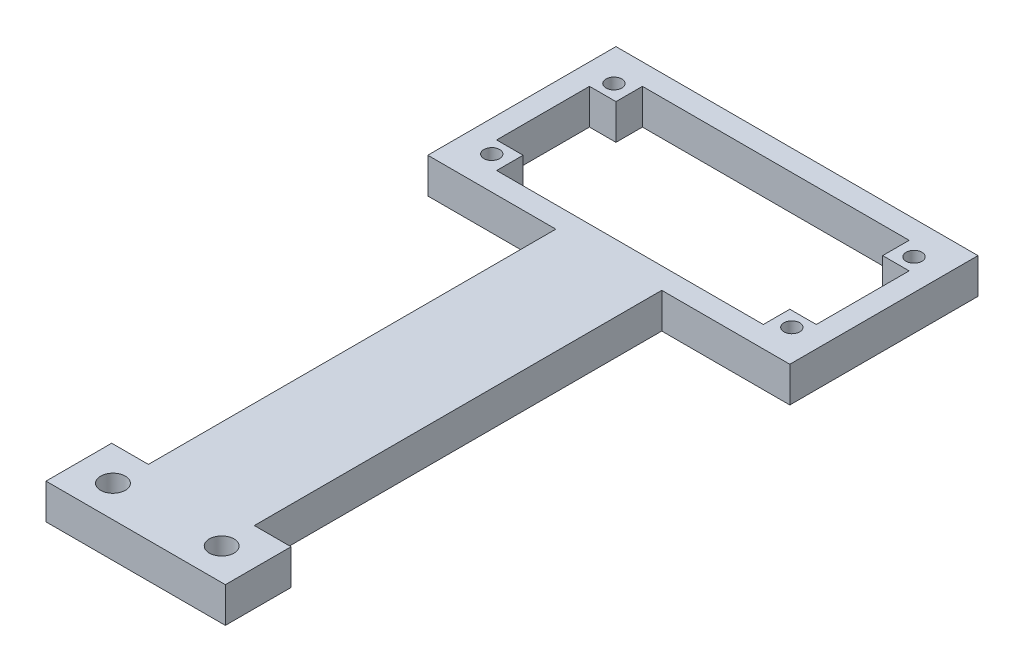
SolidWorks part; units mm, degrees
ref_plane "Front Plane" through (0, 0, 0) normal (0, 0, 1) x (1, 0, 0)
ref_plane "Top Plane" through (0, 0, 0) normal (0, 1, 0) x (1, 0, 0)
ref_plane "Right Plane" through (0, 0, 0) normal (1, 0, 0) x (0, 0, -1)
sketch "Sonic Sensor Reference Sketch" plane through (0, 0, 0) normal (0, 1, 0) x (1, 0, 0)
  line L1 (0, 0) -> (45.27, 0) construction
  line L2 (0, 0) -> (0, 20.65) construction
  line L3 (0, 20.65) -> (45.27, 20.65) construction
  line L4 (45.27, 0) -> (45.27, 20.65) construction
  dimension "D1" = 45.27
  dimension "D2" = 20.65
sketch "Sketch2" plane through (0, 0, 0) normal (0, 1, 0) x (1, 0, 0)
  line L8 (48.27, -3) -> (48.27, 23.65)
  line L9 (-3, -3) -> (48.27, -3)
  line L10 (-3, 23.65) -> (-3, -3)
  line L11 (48.27, 23.65) -> (-3, 23.65)
  line L12 (48.27, -3) -> (48.27, 23.65)
  line L13 (-3, -3) -> (48.27, -3)
  line L14 (-3, 23.65) -> (-3, -3)
  line L15 (48.27, 23.65) -> (-3, 23.65)
  dimension "D1" = 3
extrude "Boss-Extrude2" add sketch "Sketch2" along normal blind 5
sketch "Sketch3" plane through (0, 5, 0) normal (0, 1, 0) x (1, 0, 0)
  line L0 (0, 0) -> (45.27, 0) construction
  line L1 (45.27, 0) -> (45.27, 20.65) construction
  line L2 (0, 20.65) -> (45.27, 20.65) construction
  line L3 (0, 0) -> (0, 20.65) construction
  line L4 (0, 0) -> (45.27, 0)
  line L5 (45.27, 0) -> (45.27, 20.65)
  line L6 (0, 20.65) -> (45.27, 20.65)
  line L7 (0, 0) -> (0, 20.65)
extrude "Cut-Extrude1" cut sketch "Sketch3" against normal through all
sketch "Sketch4" plane through (0, 5, 0) normal (0, 1, 0) x (1, 0, 0)
  line L0 (1.385, 18.975) -> (43.885, 18.975) construction
  line L1 (22.635, 23.65) -> (22.635, -3) construction
  line L2 (48.27, 23.65) -> (-3, 23.65) construction
  line L3 (-3, -3) -> (48.27, -3) construction
  line L4 (-3, 10.325) -> (48.27, 10.325) construction
  line L5 (-3, 23.65) -> (-3, -3) construction
  line L6 (48.27, -3) -> (48.27, 23.65) construction
  line L7 (1.385, 18.975) -> (1.385, 1.675) construction
  line L8 (1.385, 1.675) -> (43.885, 1.675) construction
  line L9 (43.885, 1.675) -> (43.885, 18.975) construction
  line L11 (0, 20.65) -> (3.75, 20.65)
  line L12 (0, 20.65) -> (0, 16.9)
  line L13 (0, 16.9) -> (3.75, 16.9)
  line L14 (3.75, 20.65) -> (3.75, 16.9)
  line L15 (0, 0) -> (3.75, 0)
  line L16 (0, 0) -> (0, 3.75)
  line L17 (0, 3.75) -> (3.75, 3.75)
  line L18 (3.75, 0) -> (3.75, 3.75)
  line L19 (45.27, 0) -> (41.52, 0)
  line L20 (45.27, 0) -> (45.27, 3.75)
  line L21 (45.27, 3.75) -> (41.52, 3.75)
  line L22 (41.52, 0) -> (41.52, 3.75)
  line L23 (45.27, 20.65) -> (41.52, 20.65)
  line L24 (45.27, 20.65) -> (45.27, 16.9)
  line L25 (45.27, 16.9) -> (41.52, 16.9)
  line L26 (41.52, 20.65) -> (41.52, 16.9)
  circle A0 centre (1.385, 18.975) radius 1.12 construction
  circle A1 centre (43.885, 18.975) radius 1.12 construction
  circle A2 centre (1.385, 1.675) radius 1.12 construction
  circle A3 centre (43.885, 1.675) radius 1.12 construction
  point P17 (22.635, 18.975)
  point P18 (1.385, 10.325)
  dimension "D3" = 2.24
  dimension "D1" = 42.5
  dimension "D2" = 17.3
  dimension "D4" = 3.75
  dimension "D5" = 3.75
extrude "Boss-Extrude3" add sketch "Sketch4" against normal up to surface (5 mm away) up to face at (22.635, 0, -10.325)
sketch "Sketch5" plane through (0, 5, 0) normal (0, 1, 0) x (1, 0, 0)
  circle A0 centre (1.385, 18.975) radius 1.12
  circle A1 centre (43.885, 18.975) radius 1.12
  circle A2 centre (43.885, 1.675) radius 1.12
  circle A3 centre (1.385, 1.675) radius 1.12
  circle A4 centre (1.385, 18.975) radius 1.12 construction
  circle A5 centre (43.885, 18.975) radius 1.12 construction
  circle A6 centre (1.385, 1.675) radius 1.12 construction
  circle A7 centre (43.885, 1.675) radius 1.12 construction
extrude "Cut-Extrude2" cut sketch "Sketch5" against normal through all
sketch "Sketch6" plane through (0, 5, 0) normal (0, 1, 0) x (1, 0, 0)
  line L0 (-3, -3) -> (48.27, -3) construction
  line L1 (30.135, -3) -> (15.135, -3)
  line L2 (30.135, -3) -> (30.135, -60.7)
  line L3 (30.135, -60.7) -> (15.135, -60.7)
  line L4 (15.135, -3) -> (15.135, -60.7)
  point P6 (22.635, -3)
  point P7 (22.635, -3)
  dimension "D1" = 15
  dimension "D2" = 57.7
extrude "Boss-Extrude4" add sketch "Sketch6" against normal up to surface (5 mm away) up to face at (1.385, 0, -0.555)
sketch "Sketch7" plane through (0, 5, 0) normal (0, 1, 0) x (1, 0, 0)
  line L0 (15.135, -60.7) -> (30.135, -60.7) construction
  line L1 (9.935, -60.7) -> (35.335, -60.7)
  line L2 (9.935, -60.7) -> (9.935, -70.2)
  line L3 (9.935, -70.2) -> (35.335, -70.2)
  line L4 (35.335, -60.7) -> (35.335, -70.2)
  point P4 (22.635, -60.7)
  point P7 (22.635, -60.7)
  dimension "D1" = 25.4
  dimension "D2" = 9.5
extrude "Boss-Extrude5" add sketch "Sketch7" against normal up to surface (5 mm away) up to face at (1.385, 0, -0.555)
sketch "Sketch11" plane through (0, 0, 0) normal (0, -1, 0) x (1, 0, 0)
  circle A0 centre (30.335, 65.5178) radius 1.75
  circle A1 centre (14.935, 65.5178) radius 1.75
  dimension "D1" = 3.5
  dimension "D2" = 3.5
extrude "Cut-Extrude5" cut sketch "Sketch11" against normal through all
sketch "Sketch12" plane through (0, 5, 0) normal (0, 1, 0) x (1, 0, 0)
  line L0 (35.335, -70.2) -> (35.335, -60.7) construction
  line L1 (9.935, -70.2) -> (35.335, -70.2)
  line L2 (9.935, -70.2) -> (9.935, -70)
  line L3 (9.935, -70) -> (35.335, -70)
  line L4 (35.335, -70.2) -> (35.335, -70)
  dimension "D1" = 0.2
extrude "Cut-Extrude6" cut sketch "Sketch12" against normal through all
